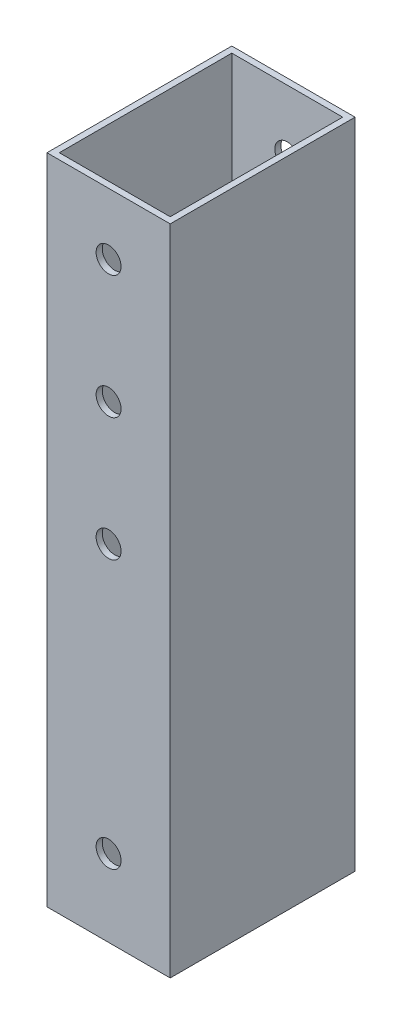
SolidWorks part; units mm, degrees
material "6063-T5"
ref_plane "前视基准面" through (0, 0, 0) normal (0, 0, 1) x (1, 0, 0)
ref_plane "上视基准面" through (0, 0, 0) normal (0, 1, 0) x (1, 0, 0)
ref_plane "右视基准面" through (0, 0, 0) normal (1, 0, 0) x (0, 0, -1)
other "Configuration Table"
sketch "草图2" plane through (0, 0, 0) normal (0, 1, 0) x (1, 0, 0)
  line L1 (-10, -15) -> (10, -15)
  line L2 (-10, -15) -> (-10, 15)
  line L3 (-10, 15) -> (10, 15)
  line L4 (10, -15) -> (10, 15)
  line L5 (-10, -15) -> (10, 15) construction
  line L6 (-10, 15) -> (10, -15) construction
  point P0 (0, 0)
  dimension "D1" = 30
  dimension "D2" = 20
extrude "凸台-拉伸1" add sketch "草图2" along normal mid plane 120
sketch "草图3" plane through (0, 0, 0) normal (0, 1, 0) x (1, 0, 0)
  line L8 (9, -14) -> (9, 14)
  line L9 (9, 14) -> (-9, 14)
  line L10 (-9, 14) -> (-9, -14)
  line L11 (-9, -14) -> (9, -14)
  line L12 (9, -14) -> (9, 14)
  line L13 (9, 14) -> (-9, 14)
  line L14 (-9, 14) -> (-9, -14)
  line L15 (-9, -14) -> (9, -14)
  dimension "D1" = 1
extrude "切除-拉伸1" cut sketch "草图3" against normal through all both and the other way through all
sketch "草图5" plane through (0, 0, 15) normal (0, 0, 1) x (1, 0, 0)
  line L0 (10, 60) -> (10, -60) construction
  line L1 (-10, -60) -> (10, -60)
  line L2 (-10, -60) -> (-10, -46)
  line L3 (-10, -46) -> (10, -46)
  line L4 (10, -60) -> (10, -46)
  dimension "D1" = 14
extrude "切除-拉伸3" cut sketch "草图5" against normal through all both and the other way through all
sketch "草图6" plane through (0, 0, 15) normal (0, 0, 1) x (1, 0, 0)
  line L0 (10, 60) -> (10, -46) construction
  line L1 (-10, -46) -> (10, -46) construction
  circle A9 centre (0, -33.5) radius 2.025
  point P2 (0, -39.6899)
  dimension "D1" = 4.05
  dimension "D2" = 10
  dimension "D3" = 12.5
extrude "切除-拉伸4" cut sketch "草图6" against normal through all
sketch "草图7" plane through (0, 0, 15) normal (0, 0, 1) x (1, 0, 0)
  line L0 (-10, 60) -> (10, 60) construction
  line L1 (10, 60) -> (10, -46) construction
  circle A0 centre (0, 50) radius 2.025
  circle A1 centre (0, 30) radius 2.025
  circle A2 centre (0, 10) radius 2.025
  dimension "D1" = 4.05
  dimension "D2" = 10
  dimension "D3" = 20
  dimension "D4" = 20
  dimension "D5" = 10
extrude "切除-拉伸5" cut sketch "草图7" against normal through all both
